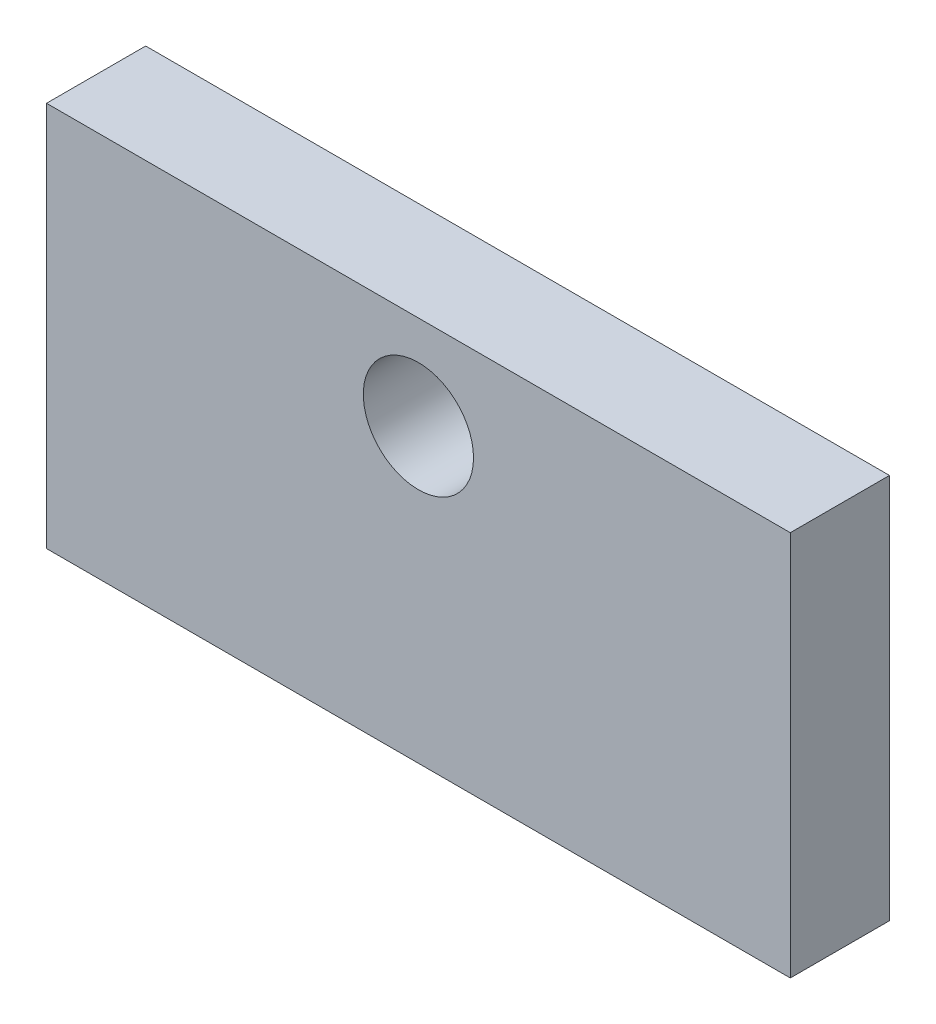
SolidWorks part; units mm, degrees
ref_plane "Alzado" through (0, 0, 0) normal (0, 0, 1) x (1, 0, 0)
ref_plane "Planta" through (0, 0, 0) normal (0, 1, 0) x (1, 0, 0)
ref_plane "Vista lateral" through (0, 0, 0) normal (1, 0, 0) x (0, 0, -1)
sketch "Croquis1" plane through (0, 0, 0) normal (0, 0, 1) x (1, 0, 0)
  line L0 (0, 0) -> (0, 70)
  line L1 (0, 70) -> (135, 70)
  line L2 (135, 70) -> (135, 0)
  line L3 (135, 0) -> (0, 0)
  dimension "D1" = 70
  dimension "D2" = 135
extrude "Saliente-Extruir1" add sketch "Croquis1" along normal blind 18
sketch "Croquis3" plane through (0, 0, 18) normal (0, 0, 1) x (1, 0, 0)
  line L0 (67.5, 70) -> (67.5, 53) construction
  line L1 (135, 70) -> (0, 70) construction
  line L2 (67.5, 53) -> (0, 53) construction
  line L3 (0, 70) -> (0, 0) construction
  circle A0 centre (67.5, 53) radius 10
  dimension "D1" = 67.5
  dimension "D2" = 17
extrude "Cortar-Extruir1" cut sketch "Croquis3" against normal through all
